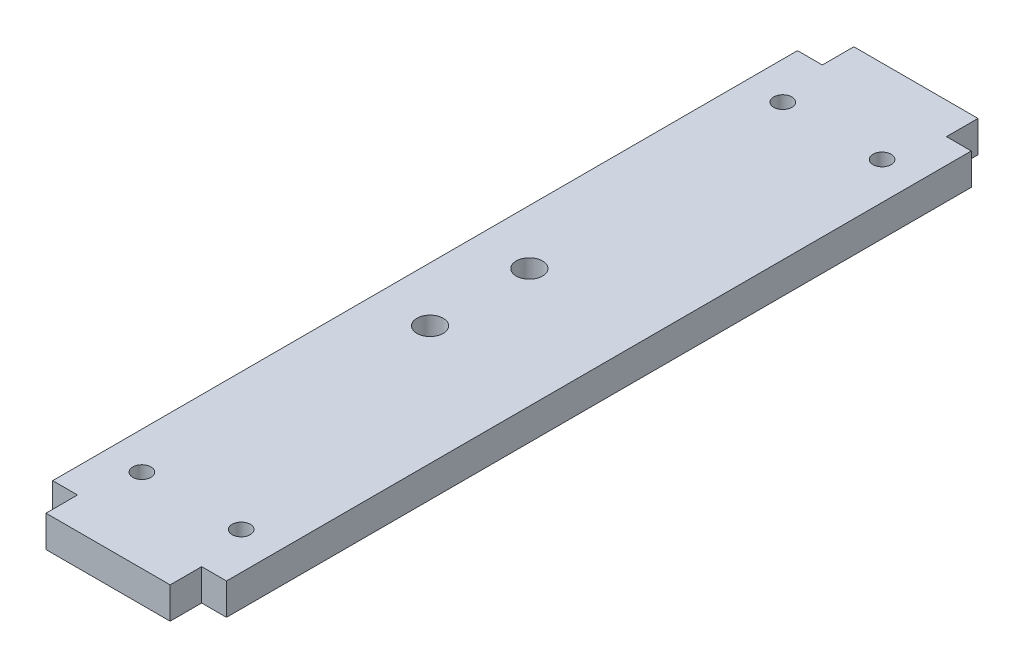
SolidWorks part; units mm, degrees
ref_plane "Front Plane" through (0, 0, 0) normal (0, 0, 1) x (1, 0, 0)
ref_plane "Top Plane" through (0, 0, 0) normal (0, 1, 0) x (1, 0, 0)
ref_plane "Right Plane" through (0, 0, 0) normal (1, 0, 0) x (0, 0, -1)
sketch "Sketch1" plane through (0, 0, 0) normal (0, 1, 0) x (1, 0, 0)
  line L1 (17.5, -75) -> (-17.5, -75)
  line L2 (17.5, -75) -> (17.5, 75)
  line L3 (17.5, 75) -> (-17.5, 75)
  line L4 (-17.5, -75) -> (-17.5, 75)
  line L5 (17.5, -75) -> (-17.5, 75) construction
  line L6 (17.5, 75) -> (-17.5, -75) construction
  point P0 (0, 0)
  dimension "D1" = 150
  dimension "D2" = 35
extrude "Boss-Extrude1" add sketch "Sketch1" along normal blind 6.35
sketch "Sketch2" plane through (0, 6.35, 0) normal (0, 1, 0) x (1, 0, 0)
  line L0 (-17.5, -75) -> (17.5, -75) construction
  line L1 (-12.5, -81.35) -> (12.5, -81.35)
  line L2 (-12.5, -81.35) -> (-12.5, -75)
  line L3 (-12.5, -75) -> (12.5, -75)
  line L4 (12.5, -81.35) -> (12.5, -75)
  line L5 (-12.5, -81.35) -> (12.5, -75) construction
  line L6 (-12.5, -75) -> (12.5, -81.35) construction
  line L7 (17.5, 75) -> (-17.5, 75) construction
  line L8 (-12.5, 81.35) -> (12.5, 81.35)
  line L9 (-12.5, 81.35) -> (-12.5, 75)
  line L10 (-12.5, 75) -> (12.5, 75)
  line L11 (12.5, 81.35) -> (12.5, 75)
  line L12 (-12.5, 81.35) -> (12.5, 75) construction
  line L13 (-12.5, 75) -> (12.5, 81.35) construction
  point P0 (0, -78.175)
  point P7 (0, 78.175)
  dimension "D1" = 25
  dimension "D2" = 6.35
extrude "Boss-Extrude2" add sketch "Sketch2" against normal blind 6.35
sketch "Sketch3" plane through (0, 6.35, 0) normal (0, 1, 0) x (1, 0, 0)
  line L0 (-10, 64.5352) -> (10, 64.5352) construction
  line L1 (-10, -64.5352) -> (10, -64.5352) construction
  line L2 (-12.5, 75) -> (-17.5, 75) construction
  line L3 (-17.5, -75) -> (-12.5, -75) construction
  point P4 (0, 64.5352)
  point P5 (0, -64.5352)
  dimension "D1" = 20
  dimension "D2" = 10.4648
  dimension "D3" = 10.4648
hole_wizard "#6 Clearance Hole1" positions "3DSketch1" profile "Sketch4" hole size "#6" standard "ANSI Inch" end condition through all
sketch3d "3DSketch1"
  point P0 (-10, 6.35, -64.5352)
  point P3 (10, 6.35, -64.5352)
  point P6 (10, 6.35, 64.5352)
  point P9 (-10, 6.35, 64.5352)
sketch "Sketch4" plane through (-10, 6.35, -64.5352) normal (1, 0, 0) x (0, 0, 1)
  line L0 (0, 0) -> (0, 6.35)
  line L1 (0, 6.35) -> (1.8288, 6.35)
  line L2 (1.8288, 6.35) -> (1.8288, 0)
  line L5 (1.8288, 0) -> (0, 0)
  line L11 (0, -6.35) -> (0, 107.95) construction
  dimension "Thru Hole Dia." = 3.6576
  dimension "Thru Hole Depth" = 6.35
sketch "Sketch5" plane through (0, 6.35, 0) normal (0, 1, 0) x (1, 0, 0)
  line L0 (-6.5, 10) -> (-6.5, -10) construction
  point P2 (-6.5, 0)
  dimension "D1" = 20
  dimension "D2" = 6.5
hole_wizard "M5 Clearance Hole1" positions "3DSketch2" profile "Sketch6" hole size "M5" standard "ANSI Metric" end condition through all
sketch3d "3DSketch2"
  point P0 (-6.5, 6.35, 10)
  point P3 (-6.5, 6.35, -10)
sketch "Sketch6" plane through (-6.5, 6.35, 10) normal (1, 0, 0) x (0, 0, 1)
  line L0 (0, 0) -> (0, 6.35)
  line L1 (0, 6.35) -> (2.65, 6.35)
  line L2 (2.65, 6.35) -> (2.65, 0)
  line L5 (2.65, 0) -> (0, 0)
  line L11 (0, -6.35) -> (0, 107.95) construction
  dimension "Thru Hole Dia." = 5.3
  dimension "Thru Hole Depth" = 6.35
